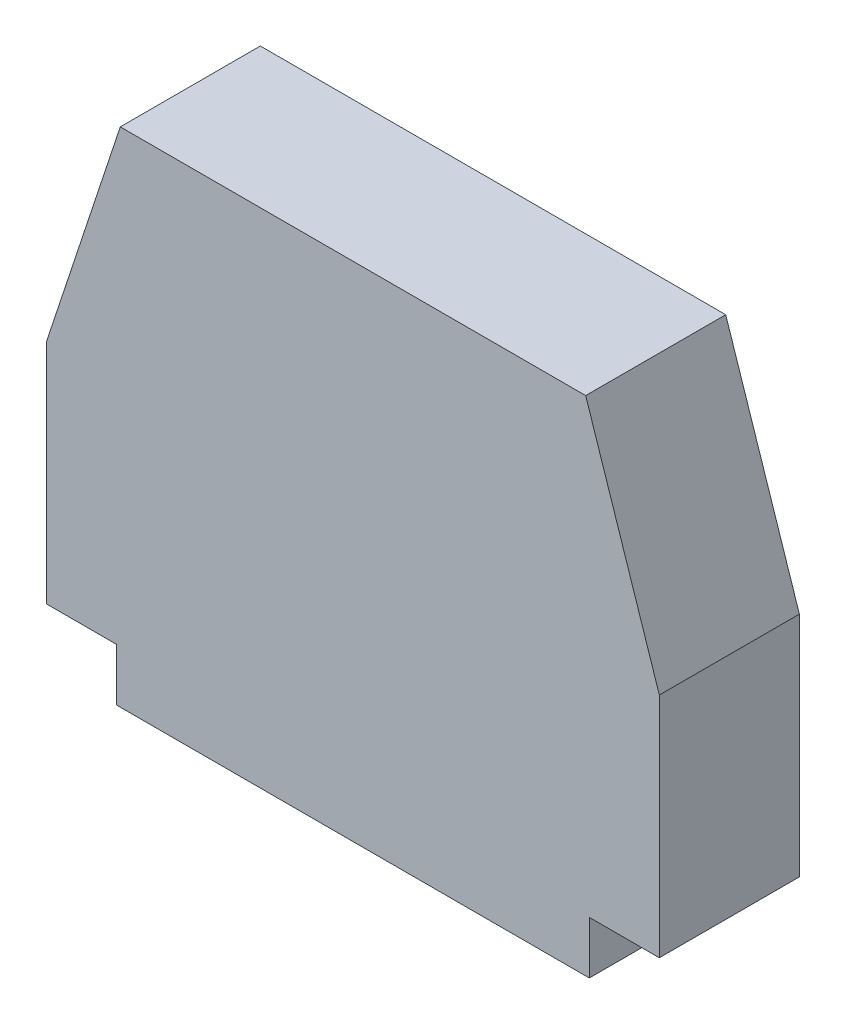
SolidWorks part; units mm, degrees
material "Стекло"
ref_plane "Спереди" through (0, 0, 0) normal (0, 0, 1) x (1, 0, 0)
ref_plane "Сверху" through (0, 0, 0) normal (0, 1, 0) x (1, 0, 0)
ref_plane "Справа" through (0, 0, 0) normal (1, 0, 0) x (0, 0, -1)
sketch "Эскиз1" plane through (0, 0, 0) normal (0, 0, 1) x (1, 0, 0)
  line L0 (0, 70.1452) -> (0, -67.2344) construction
  line L1 (-13.5, 0) -> (13.5, 0)
  line L2 (-17.5, 3) -> (-17.5, 16)
  line L3 (17.5, 3) -> (17.5, 16)
  line L4 (-17.5, 16) -> (-13.2924, 28.7088)
  line L5 (17.5, 16) -> (13.2924, 28.7088)
  line L6 (-13.2924, 28.7088) -> (13.2924, 28.7088)
  line L7 (-31.0268, 3) -> (23.3652, 3) construction
  line L8 (-17.5, 3) -> (-13.5, 3)
  line L9 (-13.5, 3) -> (-13.5, 0)
  line L10 (17.5, 3) -> (13.5, 3)
  line L11 (13.5, 3) -> (13.5, 0)
  dimension "D1" = 16
  dimension "D2" = 4
  dimension "D3" = 18.318
  dimension "D4" = 26.5849
  dimension "D5" = 3
  dimension "D6" = 4
extrude "Бобышка-Вытянуть1" add sketch "Эскиз1" along normal blind 8
